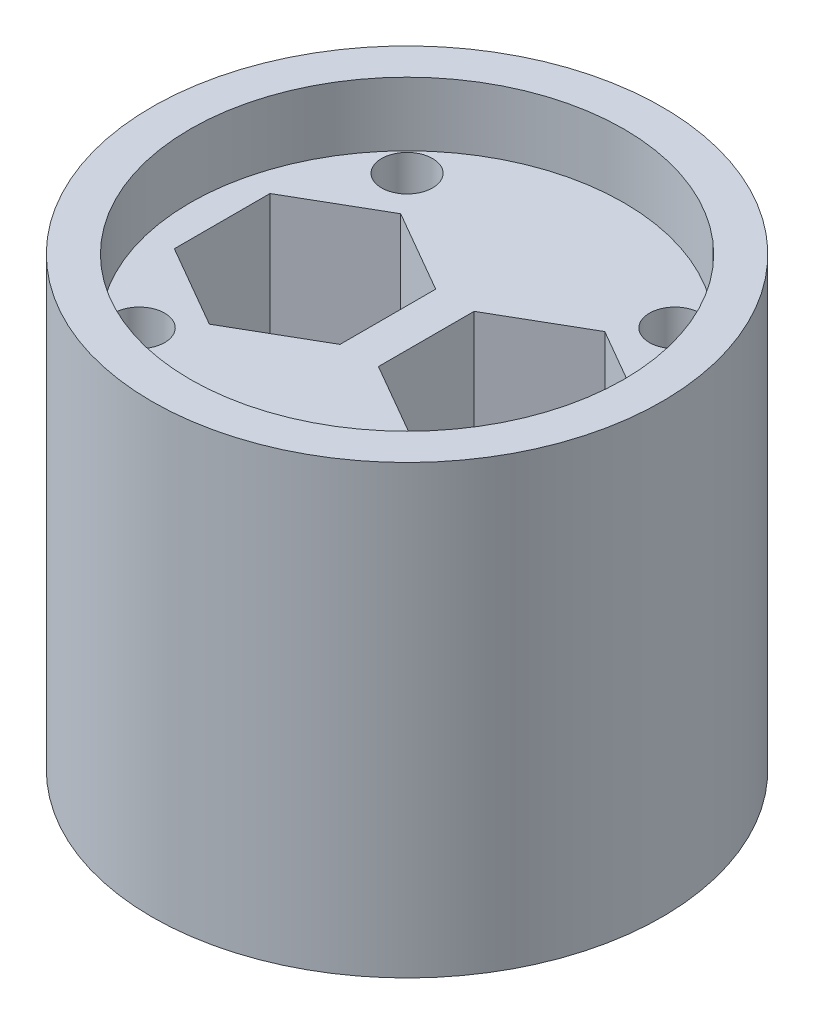
SolidWorks part; units mm, degrees
ref_plane "Спереди" through (0, 0, 0) normal (0, 0, 1) x (1, 0, 0)
ref_plane "Сверху" through (0, 0, 0) normal (0, 1, 0) x (1, 0, 0)
ref_plane "Справа" through (0, 0, 0) normal (1, 0, 0) x (0, 0, -1)
sketch "Sketch1" plane through (0, 0, 0) normal (0, 1, 0) x (1, 0, 0)
  line L1 (14.1421, -14.1421) -> (-14.1421, -14.1421) construction
  line L2 (14.1421, -14.1421) -> (14.1421, 14.1421) construction
  line L3 (14.1421, 14.1421) -> (-14.1421, 14.1421) construction
  line L4 (-14.1421, -14.1421) -> (-14.1421, 14.1421) construction
  line L5 (14.1421, -14.1421) -> (-14.1421, 14.1421) construction
  line L6 (14.1421, 14.1421) -> (-14.1421, -14.1421) construction
  circle A0 centre (0, 0) radius 20
  point P0 (0, 0)
  dimension "D1" = 40
extrude "Boss-Extrude1" add sketch "Sketch1" along normal blind 35
sketch "Sketch2" plane through (0, 35, 0) normal (0, 1, 0) x (1, 0, 0)
  line L0 (-20, 0) -> (20, 0) construction
  line L1 (-8, 7.5) -> (-14.4952, 3.75)
  line L2 (-14.4952, 3.75) -> (-14.4952, -3.75)
  line L3 (-14.4952, -3.75) -> (-8, -7.5)
  line L4 (-8, -7.5) -> (-1.5048, -3.75)
  line L5 (-1.5048, -3.75) -> (-1.5048, 3.75)
  line L6 (-1.5048, 3.75) -> (-8, 7.5)
  line L8 (8, 7.5) -> (1.5048, 3.75)
  line L9 (1.5048, 3.75) -> (1.5048, -3.75)
  line L10 (1.5048, -3.75) -> (8, -7.5)
  line L11 (8, -7.5) -> (14.4952, -3.75)
  line L12 (14.4952, -3.75) -> (14.4952, 3.75)
  line L13 (14.4952, 3.75) -> (8, 7.5)
  circle A0 centre (-8, 0) radius 7.5 construction
  circle A1 centre (0, 0) radius 20 construction
  circle A2 centre (8, 0) radius 7.5 construction
  point P10 (0, 0)
  point P23 (0, 0)
  point P24 (0, 0)
  point P25 (0, 0)
  dimension "D1" = 15
  dimension "D2" = 16
  dimension "D3" = 8
extrude "Cut-Extrude1" cut sketch "Sketch2" against normal blind 15
sketch "Sketch3" plane through (0, 20, 0) normal (0, 1, 0) x (1, 0, 0)
  line L0 (-8, 7.5) -> (-8, -7.5) construction
  line L1 (8, 7.5) -> (8, -7.5) construction
  circle A0 centre (-8, 0) radius 4.1
  circle A1 centre (8, 0) radius 4.1
  point P12 (-8, 0)
  dimension "D1" = 8.2
extrude "Cut-Extrude2" cut sketch "Sketch3" against normal through all
sketch "Sketch4" plane through (0, 35, 0) normal (0, 1, 0) x (1, 0, 0)
  line L1 (10.5, -10.5) -> (-10.5, -10.5) construction
  line L2 (10.5, -10.5) -> (10.5, 10.5) construction
  line L3 (10.5, 10.5) -> (-10.5, 10.5) construction
  line L4 (-10.5, -10.5) -> (-10.5, 10.5) construction
  line L5 (10.5, -10.5) -> (-10.5, 10.5) construction
  line L6 (10.5, 10.5) -> (-10.5, -10.5) construction
  circle A0 centre (-10.5, 10.5) radius 2
  circle A1 centre (10.5, 10.5) radius 2
  circle A2 centre (10.5, -10.5) radius 2
  circle A3 centre (-10.5, -10.5) radius 2
  point P0 (0, 0)
  dimension "D1" = 4
  dimension "D2" = 21
extrude "Cut-Extrude3" cut sketch "Sketch4" against normal through all
sketch "Sketch5" plane through (0, 35, 0) normal (0, 1, 0) x (1, 0, 0)
  circle A0 centre (0, 0) radius 17
  circle A1 centre (0, 0) radius 20 construction
  point P5 (0, 0)
  point P6 (0, 0)
  point P7 (1.5048, 2.3648)
  point P10 (1.5048, 9.3483)
  dimension "D1" = 3
extrude "Cut-Extrude4" cut sketch "Sketch5" against normal blind 5
